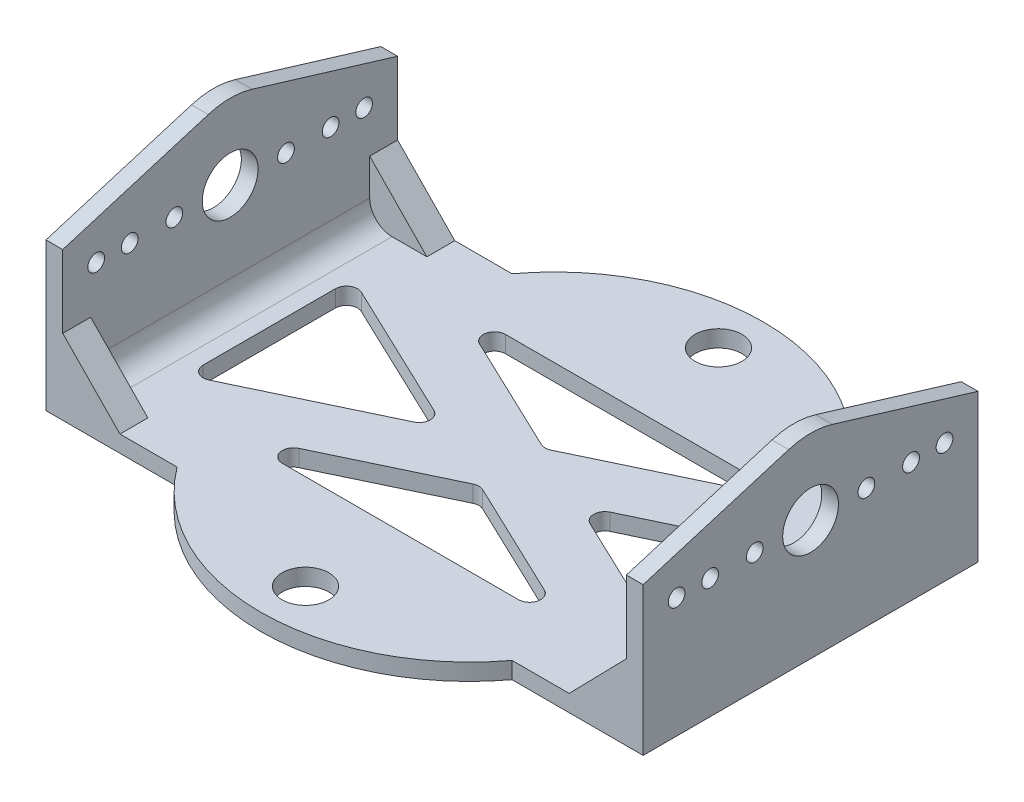
SolidWorks part; units mm, degrees
ref_plane "Front Plane" through (0, 0, 0) normal (0, 0, 1) x (1, 0, 0)
ref_plane "Top Plane" through (0, 0, 0) normal (0, 1, 0) x (1, 0, 0)
ref_plane "Right Plane" through (0, 0, 0) normal (1, 0, 0) x (0, 0, -1)
sketch "Sketch1" plane through (0, 0, 0) normal (0, 1, 0) x (1, 0, 0)
  line L0 (-53.5, 30) -> (-53.5, 67)
  line L1 (0, 0) -> (-107, 0)
  line L2 (0, 0) -> (0, 60)
  line L3 (0, 60) -> (-107, 60)
  line L4 (-107, 0) -> (-107, 60)
  line L5 (-107, 30) -> (0, 30)
  line L6 (-53.5, 60) -> (-83.5, 60)
  line L7 (-72.5027, 60) -> (-53.5, 60)
  line L8 (-53.5, 60) -> (-23.5, 60)
  line L9 (-53.5, 60) -> (-53.5, 75)
  line L10 (-97, 45) -> (-23.5, 10)
  line L11 (-97, 10) -> (-10, 10)
  line L12 (-97, 10) -> (-97, 50)
  line L13 (-97, 50) -> (-10, 50)
  line L14 (-10, 10) -> (-10, 50)
  line L15 (-97, 10) -> (-10, 50) construction
  line L16 (-97, 50) -> (-10, 10) construction
  line L17 (-97, 15) -> (-23.5, 50)
  line L18 (-10, 15) -> (-83.5, 50)
  line L19 (-10, 45) -> (-83.5, 10)
  line L20 (-53.5, 60) -> (-53.5, 0)
  line L21 (-83.5, 50) -> (-53.5, 35.7143)
  line L22 (-97, 45) -> (-53.5, 24.2857)
  circle A0 centre (-53.5, 67) radius 4.2
  arc A1 (-83.5, 60) -> (-23.5, 60) centre (-53.5, 37.6061) cw
  circle A2 centre (-53.5, -7) radius 4.2
  arc A3 (-83.5, 0) -> (-23.5, 0) centre (-53.5, 22.3939) ccw
  dimension "D4" = 8.4
  dimension "D5" = 30
  dimension "D8" = 10
  dimension "D1" = 60
  dimension "D2" = 107
  dimension "D3" = 37
  dimension "D6" = 30
  dimension "D7" = 15
  dimension "D9" = 10
  dimension "D10" = 5
  dimension "D11" = 5
  dimension "D12" = 5
  dimension "D13" = 5
extrude "Boss-Extrude1" add sketch "Sketch1" along normal blind 3
fillet "Fillet1" radius 2 12 edges at (-10, 1.5, -15) (-10, 1.5, -45) (-41.5, 1.5, -30) (-83.5, 1.5, -10) (-23.5, 1.5, -10) (-53.5, 1.5, -24.2857) (-97, 1.5, -45) (-97, 1.5, -15) (-65.5, 1.5, -30) (-23.5, 1.5, -50) (-83.5, 1.5, -50) (-53.5, 1.5, -35.7143)
sketch "Sketch2" plane through (-107, 0, 0) normal (-1, 0, 0) x (0, 0, 1)
  line L0 (-30, 35) -> (-30, 8)
  line L1 (-60, 3) -> (0, 3)
  line L2 (-60, 3) -> (-60, 19.1944)
  line L3 (-30, 3) -> (-30, 21.5)
  line L4 (0, 3) -> (0, 19.1944)
  line L5 (0, 21.5) -> (-60, 21.5)
  line L6 (-60, 16.5) -> (-60, 26.5)
  line L7 (-60, 26.5) -> (-33.922, 34.4177)
  line L8 (0, 26.5) -> (-26.078, 34.4177)
  line L9 (0, 16.5) -> (0, 26.5)
  line L10 (0, 16.5) -> (-26.078, 8.5823)
  line L11 (-60, 16.5) -> (-33.922, 8.5823)
  line L12 (-30, 21.5) -> (-40, 21.5)
  line L13 (-60, 21.5) -> (-54, 21.5)
  line L14 (-54, 21.5) -> (-48, 21.5)
  circle A0 centre (-30, 21.5) radius 13.5
  circle A1 centre (-40, 21.5) radius 1.5
  circle A2 centre (-54, 21.5) radius 1.5
  circle A3 centre (-48, 21.5) radius 1.5
  circle A4 centre (-20, 21.5) radius 1.5
  circle A5 centre (-12, 21.5) radius 1.5
  circle A6 centre (-6, 21.5) radius 1.5
  circle A7 centre (-30, 21.5) radius 5
  dimension "D1" = 5
extrude "Boss-Extrude2" add sketch "Sketch2" against normal blind 3
sketch "Sketch3" plane through (0, 3, 0) normal (0, 1, 0) x (1, 0, 0)
  line L0 (-53.5, 75.0425) -> (-53.5, -15.0425) construction
  arc A0 (-23.5, 60) -> (-83.5, 60) centre (-53.5, 37.6061) ccw construction
  arc A1 (-83.5, 0) -> (-23.5, 0) centre (-53.5, 22.3939) ccw construction
ref_plane "Plane1" through (-53.5, 0, 0) normal (1, 0, 0) x (0, 0, -1)
mirror "Mirror1" about plane through (-53.5, 0, 0) normal (1, 0, 0) of "Boss-Extrude2"
sketch "Sketch4" plane through (0, 0, 0) normal (0, 0, 1) x (1, 0, 0)
  line L0 (-104, 13.5) -> (-93.75, 3)
  line L1 (-104, 3) -> (-104, 26.5) construction
  line L2 (-83.5, 3) -> (-104, 3) construction
  line L3 (-104, 13.5) -> (-104, 3)
  line L4 (-104, 3) -> (-93.75, 3)
  dimension "D1" = 13
extrude "Boss-Extrude3" add sketch "Sketch4" against normal blind 5
mirror "Mirror2" about plane through (-53.5, 0, 0) normal (1, 0, 0) of "Boss-Extrude3"
ref_plane "Plane2" through (-104, 3, -5) normal (0, 0, -1) x (-1, 0, 0)
sketch "Sketch6" plane through (0, 3, 0) normal (0, 1, 0) x (1, 0, 0)
  line L0 (-97, 30) -> (-10, 30) construction
  line L1 (-97, 18.1676) -> (-97, 41.8324) construction
  line L2 (-10, 18.1676) -> (-10, 41.8324) construction
  line L3 (-10, 18.1676) -> (-10, 41.8324)
  line L4 (-97, 18.1676) -> (-97, 30)
  line L5 (-97, 30) -> (-97, 41.8324)
ref_plane "Plane3" through (0, 0, -30) normal (0, 0, 1) x (1, 0, 0)
mirror "Mirror3" about plane through (0, 0, -30) normal (0, 0, 1) of "Mirror2", "Boss-Extrude3"
fillet "Fillet2" radius 4 2 edges at (-104, 3, -30) (-3, 3, -30)
